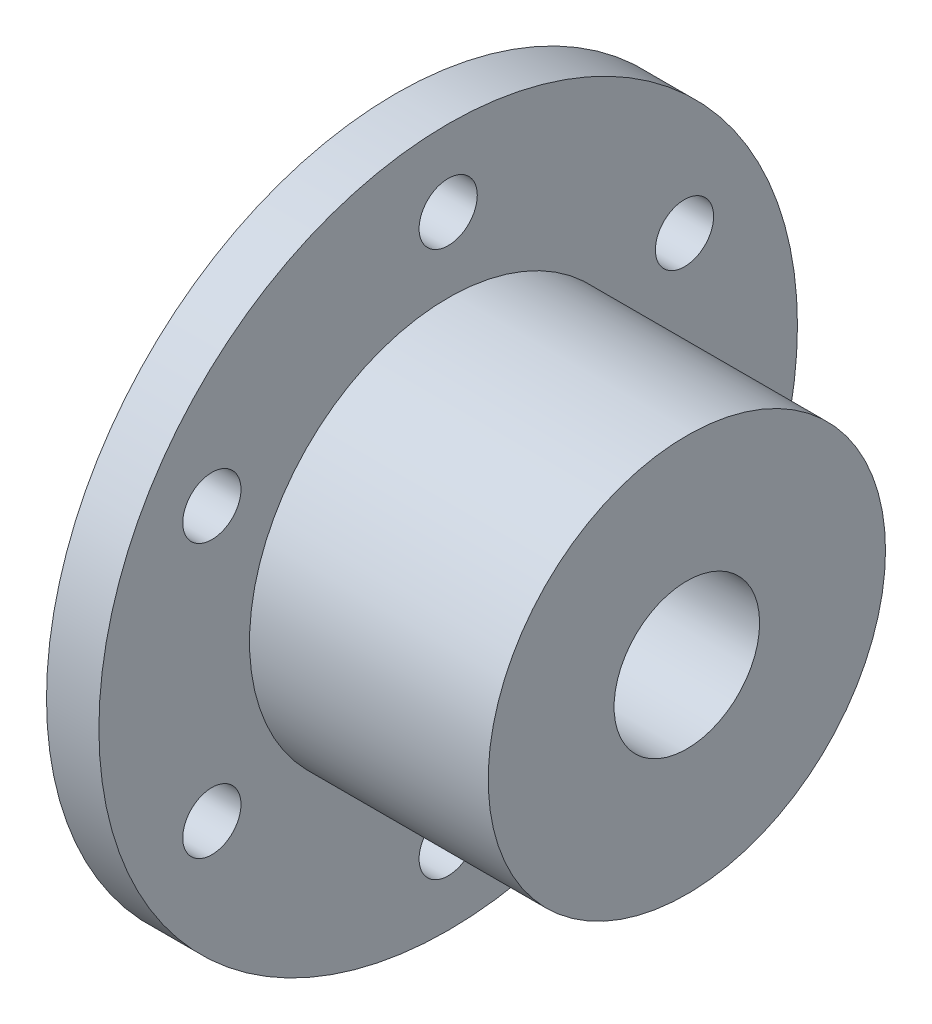
SolidWorks part; units mm, degrees
ref_plane "Front Plane" through (0, 0, 0) normal (0, 0, 1) x (1, 0, 0)
ref_plane "Top Plane" through (0, 0, 0) normal (0, 1, 0) x (1, 0, 0)
ref_plane "Right Plane" through (0, 0, 0) normal (1, 0, 0) x (0, 0, -1)
sketch "Sketch1" plane through (0, 0, 0) normal (1, 0, 0) x (0, 0, -1)
  circle A0 centre (0, 0) radius 30.48
  circle A1 centre (0, 0) radius 6.35
  circle A2 centre (0, 0) radius 23.8125 construction
  circle A3 centre (0, 23.8125) radius 2.54
  circle A4 centre (20.6222, 11.9063) radius 2.54
  circle A5 centre (20.6222, -11.9062) radius 2.54
  circle A6 centre (0, -23.8125) radius 2.54
  circle A7 centre (-20.6222, -11.9063) radius 2.54
  circle A8 centre (-20.6222, 11.9062) radius 2.54
  point P20 (0, 0)
  dimension "D1" = 6
extrude "Boss-Extrude1" add sketch "Sketch1" along normal mid plane 25.4
sketch "Sketch2" plane through (12.7, 0, 0) normal (1, 0, 0) x (0, 0, -1)
  circle A0 centre (0, 0) radius 17.3355
extrude "Cut-Extrude1" cut sketch "Sketch2" against normal blind 20.828 flip side to cut
ref_plane "Flange centre" through (-10.414, 0, 0) normal (-1, 0, 0) x (0, 0, 1)
sketch "Sketch3" plane through (12.7, 0, 0) normal (1, 0, 0) x (0, 0, -1)
  circle A0 centre (0, 0) radius 15.56
extrude "Cut-Extrude2" [suppressed] cut sketch "Sketch3" against normal through all
